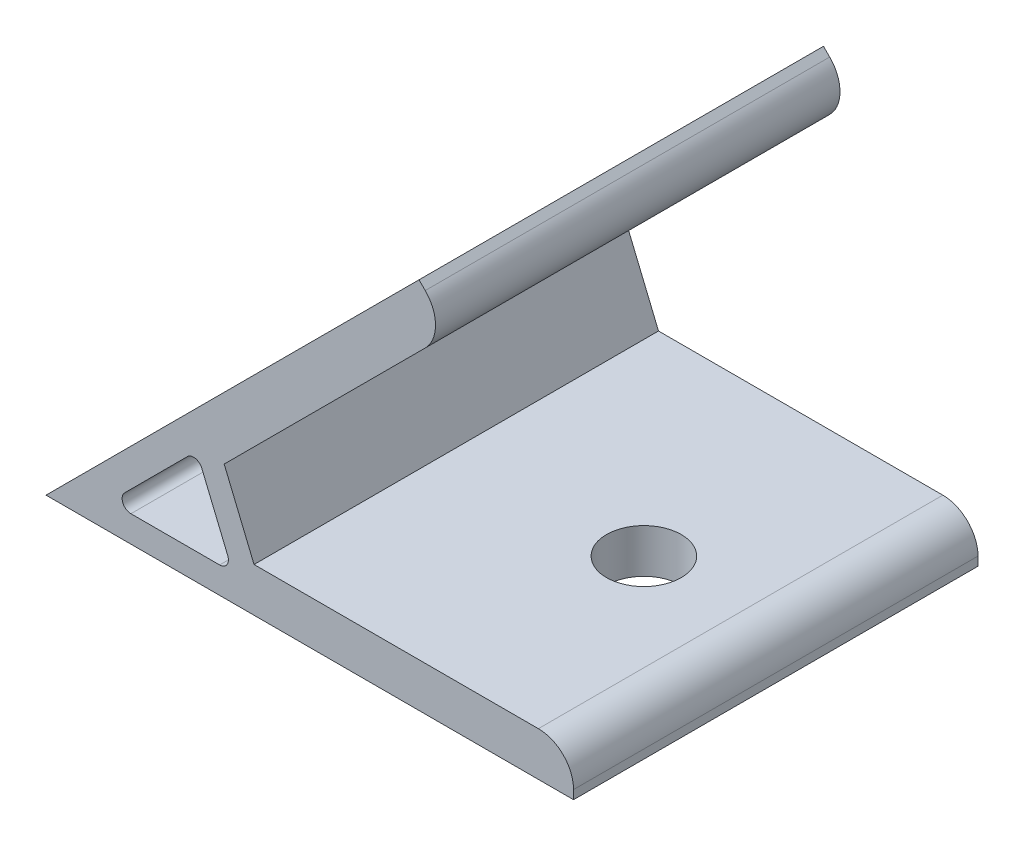
SolidWorks part; units mm, degrees
material "6063 T5"
ref_plane "Спереди" through (0, 0, 0) normal (0, 0, 1) x (1, 0, 0)
ref_plane "Сверху" through (0, 0, 0) normal (0, 1, 0) x (1, 0, 0)
ref_plane "Справа" through (0, 0, 0) normal (1, 0, 0) x (0, 0, -1)
sketch "Эскиз1" plane through (0, 0, 0) normal (0, 0, 1) x (1, 0, 0)
  line L0 (0, 0) -> (42.4264, 42.4264)
  line L1 (42.4264, 42.4264) -> (45.9619, 38.8909)
  line L2 (45.9619, 38.8909) -> (20.2667, 13.1956)
  line L3 (20.2667, 13.1956) -> (23.6614, 5)
  line L4 (23.6614, 5) -> (60, 5)
  line L5 (60, 5) -> (60, 0)
  line L6 (60, 0) -> (0, 0)
  line L7 (17.1421, 12.8995) -> (21.2426, 3)
  line L8 (21.2426, 3) -> (7.2426, 3)
  line L9 (7.2426, 3) -> (17.1421, 12.8995)
  line L10 (14.2426, 3) -> (14.2426, 0) construction
  line L11 (12.1924, 7.9497) -> (10.0711, 10.0711) construction
  line L12 (0, 0) -> (19.1924, 7.9497) construction
  point P15 (39.2751, 39.2751)
  dimension "D1" = 60
  dimension "D2" = 45
  dimension "D3" = 3
  dimension "D4" = 5
  dimension "D5" = 3
  dimension "D6" = 14
extrude "Бобышка-Вытянуть1" add sketch "Эскиз1" along normal mid plane 46
sketch "Эскиз2" plane through (0, 0, 0) normal (-0.7071, 0.7071, 0) x (0, 0, 1)
  line L0 (23, 60) -> (-23, 60) construction
  circle A0 centre (0, 45) radius 4.25
  point P2 (-2.935, 46.7791)
  dimension "D1" = 8.5
  dimension "D2" = 15
extrude "Вырез-Вытянуть1" cut sketch "Эскиз2" against normal up to surface (5 mm away) up to face at (33.1143, 26.0432, 0)
sketch "Эскиз3" plane through (0, 0, 0) normal (0, -1, 0) x (1, 0, 0)
  line L0 (60, 23) -> (60, -23) construction
  circle A0 centre (45, 0) radius 4.25
  point P2 (0, 0)
  dimension "D1" = 8.5
  dimension "D2" = 15
extrude "Вырез-Вытянуть2" cut sketch "Эскиз3" against normal up to surface (5 mm away) up to face at (41.8307, 5, 0)
fillet "Скругление1" radius 4 2 edges at (60, 5, 0) (45.9619, 38.8909, 0)
fillet "Скругление2" radius 1 3 edges at (17.1421, 12.8995, 0) (7.2426, 3, 0) (21.2426, 3, 0)
